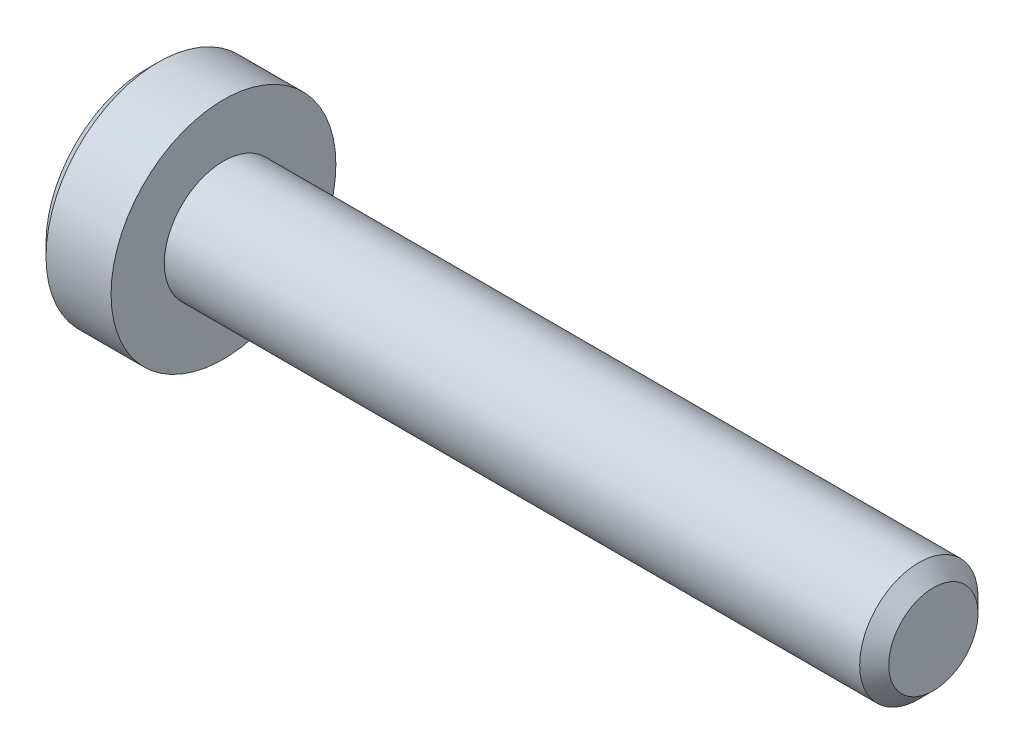
SolidWorks part; units mm, degrees
material "AISI 304"
ref_plane "正面" through (0, 0, 0) normal (0, 0, 1) x (1, 0, 0)
ref_plane "平面" through (0, 0, 0) normal (0, 1, 0) x (1, 0, 0)
ref_plane "右側面" through (0, 0, 0) normal (1, 0, 0) x (0, 0, -1)
ref_plane "Plane1" through (0, 0, 0) normal (0, 0, 1) x (1, 0, 0)
sketch "Sketch1" plane through (0, 0, 0) normal (0, 0, 1) x (1, 0, 0)
  line L0 (-1.3, 0) -> (-1.3, 1.7)
  line L1 (-1.3, 1.7) -> (-1.1, 1.9)
  line L2 (-1.1, 1.9) -> (0, 1.9)
  line L3 (0, 1.9) -> (0, 1)
  line L4 (0, 1) -> (11.7545, 1)
  line L5 (11.7545, 1) -> (12, 0.7545)
  line L6 (12, 0.7545) -> (12, 0)
  line L7 (12, 0) -> (-1.3, 0)
  line L8 (12, 0) -> (-1.3, 0) construction
revolve "Revolve1" add sketch "Sketch1" angle 360 about L8
cosmetic thread "Cosmetic Thread1" parameters "D1"=9.5748, "D2"=1.509
ref_plane "Plane2" through (-1.3, 0, 0) normal (1, 0, 0) x (0, 0, -1)
sketch "Sketch2" plane through (-1.3, 0, 0) normal (1, 0, 0) x (0, 0, -1)
  line L0 (-0.65, -0.3753) -> (0, -0.7506)
  line L1 (0, -0.7506) -> (0.65, -0.3753)
  line L2 (0.65, -0.3753) -> (0.65, 0.3753)
  line L3 (0.65, 0.3753) -> (0, 0.7506)
  line L4 (0, 0.7506) -> (-0.65, 0.3753)
  line L5 (-0.65, 0.3753) -> (-0.65, -0.3753)
extrude "Cut-Extrude1" cut sketch "Sketch2" along normal blind 0.7
